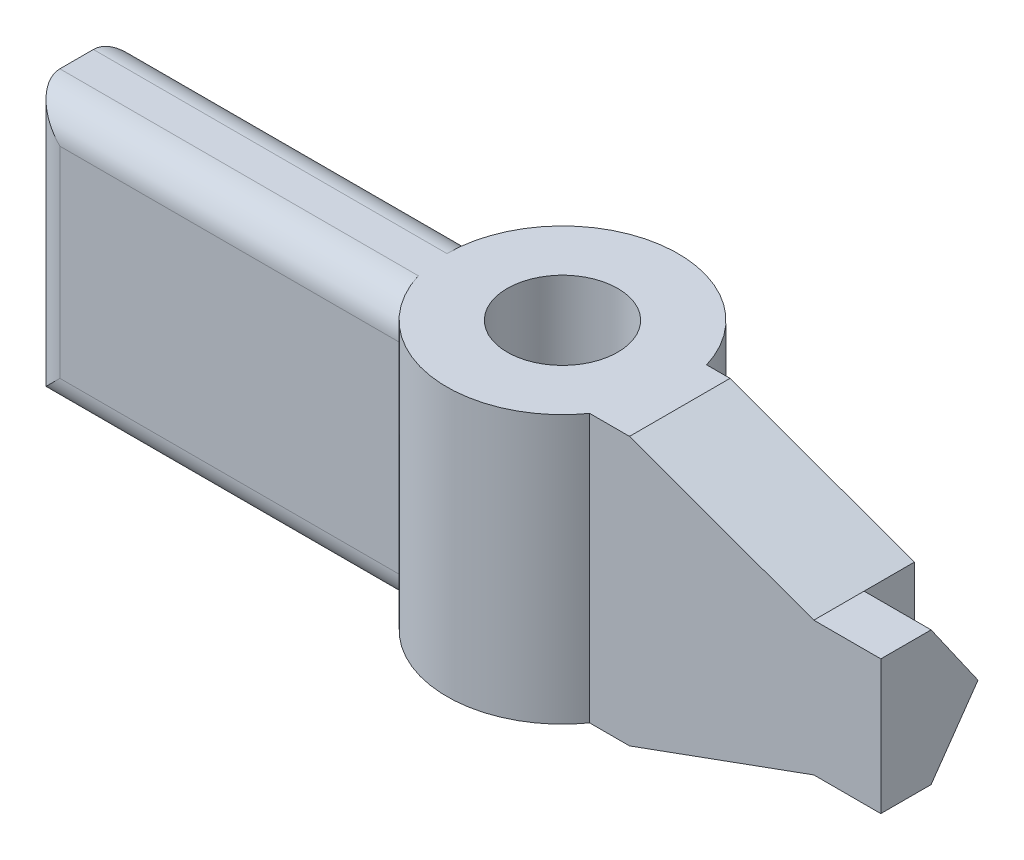
SolidWorks part; units mm, degrees
ref_plane "Front Plane" through (0, 0, 0) normal (0, 0, 1) x (1, 0, 0)
ref_plane "Top Plane" through (0, 0, 0) normal (0, 1, 0) x (1, 0, 0)
ref_plane "Right Plane" through (0, 0, 0) normal (1, 0, 0) x (0, 0, -1)
sketch "Sketch1" plane through (0, 0, 0) normal (0, 0, 1) x (1, 0, 0)
  line L0 (-2.75, 4) -> (5.25, 4)
  line L1 (5.25, 4) -> (10.75, 2)
  line L2 (10.75, 2) -> (12.75, 2)
  line L3 (5.25, -4) -> (-2.75, -4)
  line L4 (-2.75, -4) -> (-12.75, -4)
  line L5 (-12.75, -4) -> (-12.75, 4)
  line L6 (-12.75, 4) -> (-2.75, 4)
  line L7 (5.25, -4) -> (10.75, -2)
  line L8 (12.75, 2) -> (12.75, -2)
  line L10 (12.75, -2) -> (10.75, -2)
  dimension "D1" = 5.25
  dimension "D2" = 10.75
  dimension "D5" = 12.75
  dimension "D6" = 2.75
  dimension "D7" = 12.75
  dimension "D8" = 2
  dimension "D9" = 4
extrude "Boss-Extrude1" add sketch "Sketch1" along normal blind 7
sketch "Sketch2" plane through (0, 4, 0) normal (0, 1, 0) x (1, 0, 0)
  line L0 (-12.75, -7) -> (-12.75, 0) construction
  line L1 (5.25, 0) -> (-12.75, 0) construction
  line L2 (-12.75, -2.5) -> (-2.0519, -2.5)
  line L3 (-12.75, -5.5) -> (-1.5611, -5.5)
  line L4 (4.5519, -2.5) -> (12.75, -2.5)
  line L5 (4.0611, -5.5) -> (12.75, -5.5)
  line L6 (-12.75, -7) -> (12.75, -7)
  line L11 (-12.75, -7) -> (-12.75, -5.5)
  line L13 (12.75, -5.5) -> (12.75, -7)
  line L14 (12.75, 0) -> (12.75, -2.5)
  line L19 (-12.75, 0) -> (12.75, 0)
  line L20 (-12.75, -2.5) -> (-12.75, 0)
  arc A0 (-1.5611, -5.5) -> (4.0611, -5.5) centre (1.25, -3.5) ccw
  arc A1 (4.5519, -2.5) -> (-2.0519, -2.5) centre (1.25, -3.5) ccw
  circle A5 centre (1.25, -3.5) radius 1.65
extrude "Cut-Extrude1" cut sketch "Sketch2" against normal up to surface (8 mm away) up to face at (-3.75, -4, 3.5)
sketch "Sketch3" plane through (12.75, 0, 0) normal (1, 0, 0) x (0, 0, -1)
  line L0 (-4, 2) -> (-2.6, 0)
  line L1 (-4, -2) -> (-2.5, -2)
  line L2 (-4, -2) -> (-2.6, 0)
  line L3 (-2.5, -2) -> (-2.5, 0)
  line L4 (-2.5, 2) -> (-4, 2)
  line L5 (-2.5, 2) -> (-2.5, 0)
  line L6 (-5.5, -2) -> (-5.5, 2) construction
  line L7 (-5.5, 2) -> (-2.5, 2) construction
  dimension "D2" = 3
extrude "Cut-Extrude2" cut sketch "Sketch3" against normal blind 2
fillet "Fillet1" radius 1 6 edges at (-7.1556, 4, 5.5) (-12.75, 0, 5.5) (-7.1556, -4, 5.5) (-7.4009, -4, 2.5) (-12.75, 0, 2.5) (-7.4009, 4, 2.5)
